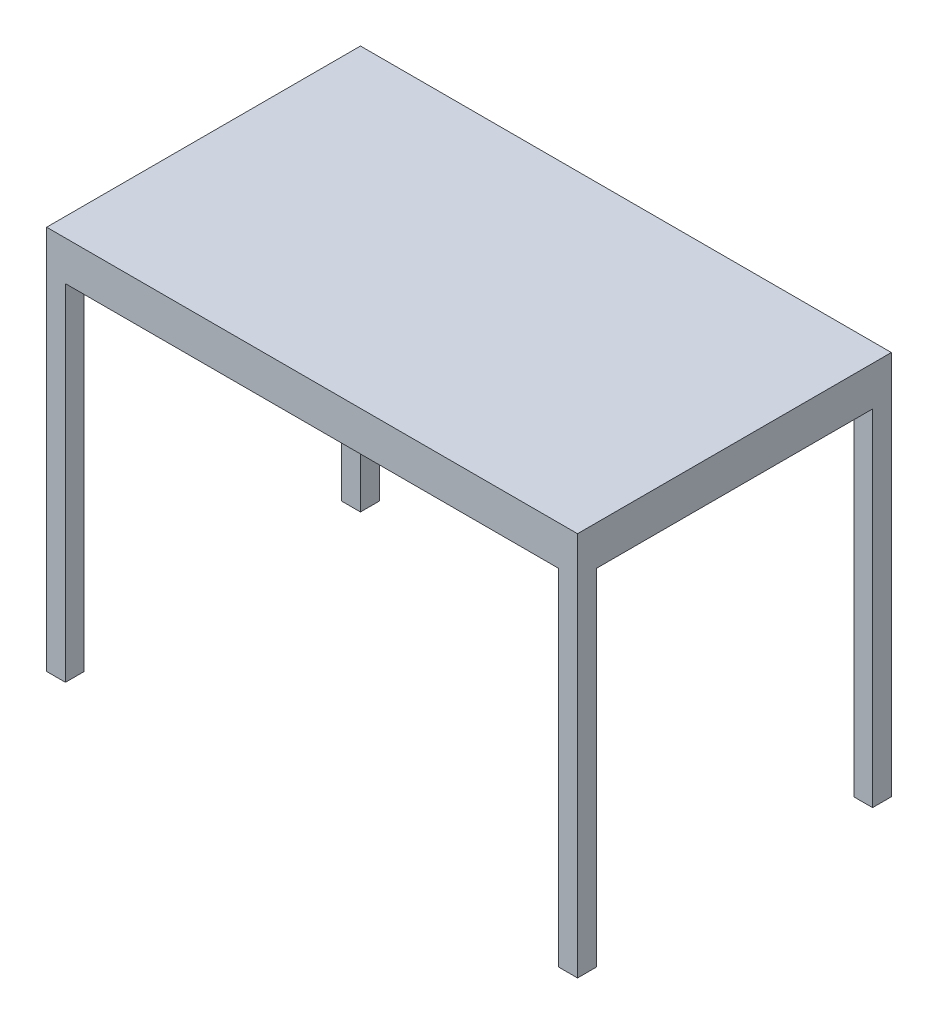
SolidWorks part; units mm, degrees
ref_plane "Alzado" through (0, 0, 0) normal (0, 0, 1) x (1, 0, 0)
ref_plane "Planta" through (0, 0, 0) normal (0, 1, 0) x (1, 0, 0)
ref_plane "Vista lateral" through (0, 0, 0) normal (1, 0, 0) x (0, 0, -1)
sketch "Croquis1" plane through (0, 0, 0) normal (0, 1, 0) x (1, 0, 0)
  line L0 (0, -38.1) -> (0, -318.1) construction
  line L1 (0, 0) -> (38.1, 0)
  line L2 (0, 0) -> (0, -38.1)
  line L3 (0, -38.1) -> (38.1, -38.1)
  line L4 (38.1, 0) -> (38.1, -38.1)
  line L5 (38.1, 0) -> (1038.1, 0) construction
  line L6 (0, -318.1) -> (166.6751, -318.1) construction
  line L7 (1038.1, 0) -> (1076.2, 0)
  line L8 (1038.1, 0) -> (1038.1, -38.1)
  line L9 (1038.1, -38.1) -> (1076.2, -38.1)
  line L10 (1076.2, 0) -> (1076.2, -38.1)
  line L11 (38.1, -636.2) -> (1038.1, -636.2) construction
  line L12 (1076.2, -636.2) -> (1076.2, -598.1)
  line L13 (1038.1, -598.1) -> (1076.2, -598.1)
  line L14 (1038.1, -636.2) -> (1038.1, -598.1)
  line L15 (1038.1, -636.2) -> (1076.2, -636.2)
  line L16 (38.1, -636.2) -> (38.1, -598.1)
  line L17 (0, -598.1) -> (38.1, -598.1)
  line L18 (0, -636.2) -> (0, -598.1)
  line L19 (0, -636.2) -> (38.1, -636.2)
  dimension "D1" = 38.1
  dimension "D2" = 38.1
  dimension "D3" = 280
  dimension "D4" = 1000
  dimension "D5" = 38.1
  dimension "D6" = 38.1
extrude "Saliente-Extruir1" add sketch "Croquis1" along normal blind 700
sketch "Croquis2" plane through (0, 700, 0) normal (0, 1, 0) x (1, 0, 0)
  line L1 (0, 0) -> (1076.2, 0)
  line L2 (0, 0) -> (0, -636.2)
  line L3 (0, -636.2) -> (1076.2, -636.2)
  line L4 (1076.2, 0) -> (1076.2, -636.2)
extrude "Saliente-Extruir2" add sketch "Croquis2" along normal blind 80
